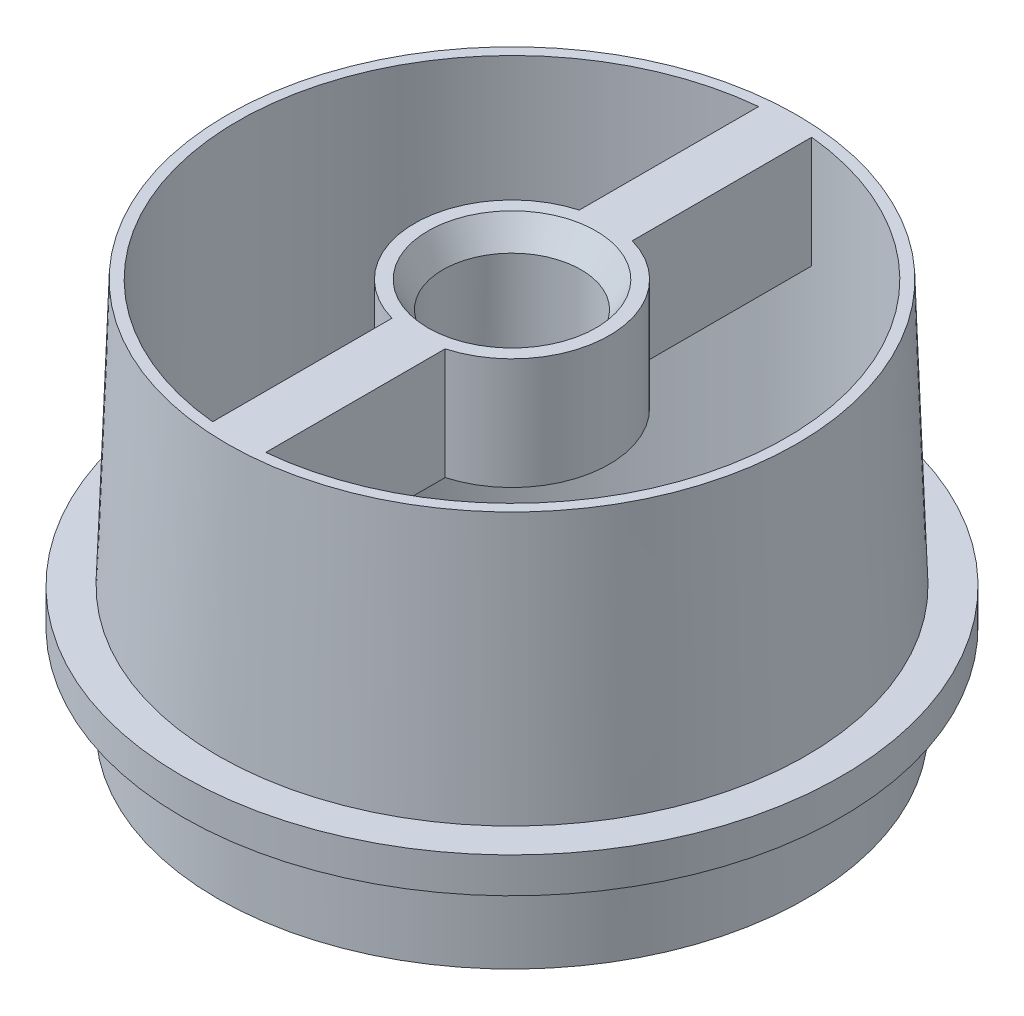
SolidWorks part; units mm, degrees
material "CA"
ref_plane "Front Plane" through (0, 0, 0) normal (0, 0, 1) x (1, 0, 0)
ref_plane "Top Plane" through (0, 0, 0) normal (0, 1, 0) x (1, 0, 0)
ref_plane "Right Plane" through (0, 0, 0) normal (1, 0, 0) x (0, 0, -1)
sketch "Sketch1" plane through (0, 0, 0) normal (0, 1, 0) x (1, 0, 0)
  circle A0 centre (0, 0) radius 15.5
  circle A1 centre (0, 0) radius 16.625
  dimension "D1" = 31
  dimension "D2" = 33.25
extrude "Boss-Extrude1" add sketch "Sketch1" along normal blind 15 draft 2
sketch "Sketch4" plane through (0, 0, 0) normal (0, 1, 0) x (1, 0, 0)
  circle A1 centre (0, 0) radius 15.5
  circle A3 centre (0, 0) radius 18.625
  circle A6 centre (0, 0) radius 16.625 construction
  dimension "D1" = 2
extrude "Boss-Extrude2" add sketch "Sketch4" against normal blind 2
sketch "Sketch5" plane through (0, -2, 0) normal (0, -1, 0) x (1, 0, 0)
  circle A0 centre (0, 0) radius 15.5
  circle A1 centre (0, 0) radius 16.625
  circle A2 centre (0, 0) radius 18.625 construction
  dimension "D1" = 2
extrude "Boss-Extrude3" add sketch "Sketch5" along normal blind 5
sketch "Sketch9" plane through (0, 0, 0) normal (0, 1, 0) x (1, 0, 0)
  circle A1 centre (0, 0) radius 15.5
  circle A2 centre (0, 0) radius 16.1012
extrude "Boss-Extrude5" add sketch "Sketch9" along normal through all
sketch "Sketch10" plane through (0, 15, 0) normal (0, 1, 0) x (1, 0, 0)
  line L0 (-1.4909, 5.2941) -> (-1.4909, 15.4281)
  line L2 (1.5091, 15.4264) -> (1.5091, 5.2889)
  line L3 (-1.4909, -5.2941) -> (-1.4909, -15.4281)
  line L5 (1.5091, -5.2889) -> (1.5091, -15.4264)
  circle A0 centre (0, 0) radius 15.5 construction
  arc A1 (-1.4909, 5.2941) -> (-1.4909, -5.2941) centre (0, 0) ccw
  arc A3 (1.5091, -5.2889) -> (1.5091, 5.2889) centre (0, 0) ccw
  arc A4 (-1.4909, 15.4281) -> (1.5091, 15.4264) centre (0, 0) cw
  arc A5 (-1.4909, -15.4281) -> (1.5091, -15.4264) centre (0, 0) ccw
  circle A6 centre (0, 0) radius 15.5 construction
  circle A7 centre (0, 0) radius 16.1012 construction
  point P7 (0, 0)
  dimension "D4" = 5.5
  dimension "D1" = 1.5091
  dimension "D2" = 1.4909
extrude "Boss-Extrude8" add sketch "Sketch10" against normal blind 6.3
sketch "Sketch11" plane through (0, 15, 0) normal (0, 1, 0) x (1, 0, 0)
  circle A0 centre (0, 0) radius 3.9
  arc A1 (1.5091, -5.2889) -> (1.5091, 5.2889) centre (0, 0) ccw construction
  dimension "D1" = 1.6
extrude "Cut-Extrude2" cut sketch "Sketch11" against normal through all
sketch "Sketch12" plane through (0, 15, 0) normal (0, 1, 0) x (1, 0, 0)
  circle A0 centre (0, 0) radius 4.75
  arc A1 (1.5091, -5.2889) -> (1.5091, 5.2889) centre (0, 0) ccw construction
  dimension "D1" = 0.75
extrude "Cut-Extrude3" cut sketch "Sketch12" against normal through all draft 30
